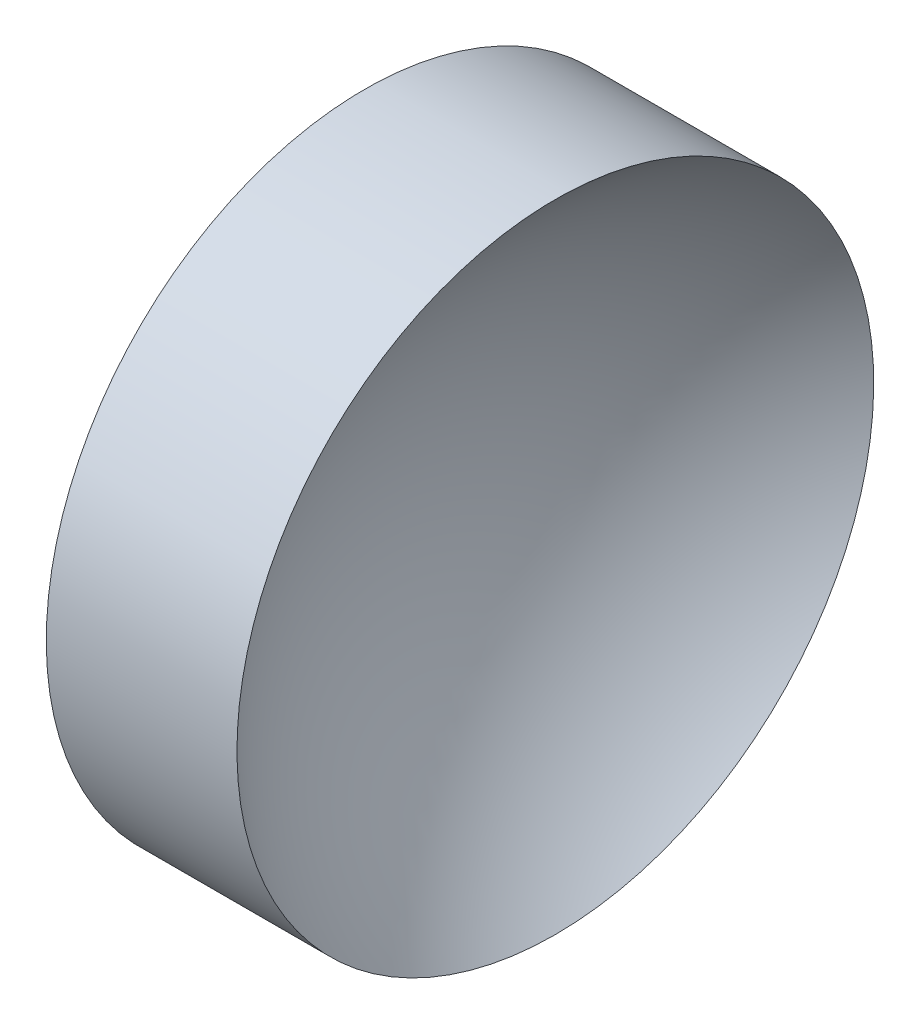
SolidWorks part; units mm, degrees
ref_plane "前视基准面" through (0, 0, 0) normal (0, 0, 1) x (1, 0, 0)
ref_plane "上视基准面" through (0, 0, 0) normal (0, 1, 0) x (1, 0, 0)
ref_plane "右视基准面" through (0, 0, 0) normal (1, 0, 0) x (0, 0, -1)
sketch "草图1" plane through (0, 0, 0) normal (0, 0, 1) x (1, 0, 0)
  line L0 (110.0148, 65.1575) -> (131.4016, 65.1575) construction
  line L1 (114.9754, 65.1575) -> (114.9754, 85.1575)
  line L2 (114.9754, 85.1575) -> (126.9537, 85.1575)
  line L3 (117.4754, 65.1575) -> (114.9754, 65.1575)
  arc A0 (126.9537, 85.1575) -> (117.4754, 65.1575) centre (143.3154, 65.1575) ccw
revolve "旋转1" add sketch "草图1" angle 360 about L0
